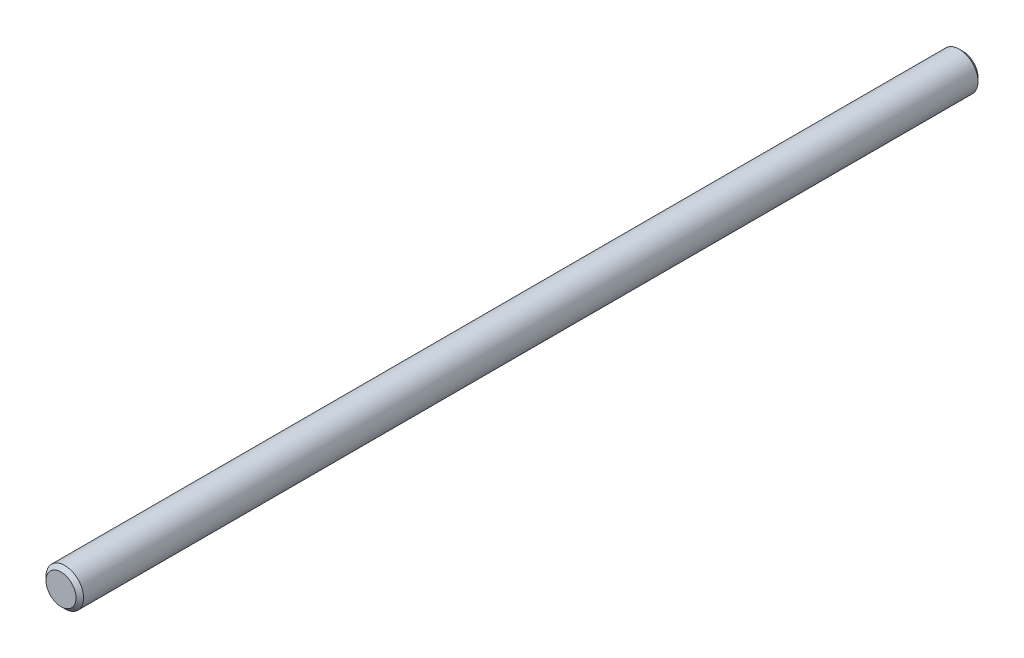
SolidWorks part; units mm, degrees
ref_plane "Front" through (0, 0, 0) normal (0, 0, 1) x (1, 0, 0)
ref_plane "Top" through (0, 0, 0) normal (0, 1, 0) x (1, 0, 0)
ref_plane "Right" through (0, 0, 0) normal (1, 0, 0) x (0, 0, -1)
sketch "Sketch1" plane through (0, 0, 0) normal (0, 0, 1) x (1, 0, 0)
  circle A0 centre (0, 0) radius 3.175
  dimension "dia" = 6.35
sketch "Sketch3" plane through (0, 0, 0) normal (0, 0, 1) x (1, 0, 0)
  circle A0 centre (0, 0) radius 3.175 construction
  circle A1 centre (0, 0) radius 3.175
extrude "Boss-Extrude1" add sketch "Sketch3" along normal mid plane 152.4
sketch "Sketch2" plane through (0, 0, 0) normal (1, 0, 0) x (0, 0, -1)
  line L0 (76.2, 3.175) -> (-76.2, 3.175) construction
  point P0 (-76.2, 3.175)
  point P1 (76.2, 3.175)
  point P2 (-63.5, 3.175)
  point P3 (63.5, 3.175)
  dimension "D1" = 12.7
  dimension "D2" = 12.7
chamfer "Chamfer1" distance 0.635 angle 45 2 edges at (3.175, 0, 76.2) (3.175, 0, -76.2)
equation "\"D1@Chamfer1\" = \"dia@Sketch1\" / 10"
equation "\"D1@Sketch2\"=\"dia@Sketch1\"*2"
equation "\"D2@Sketch2\"=\"D1@Sketch2\""
